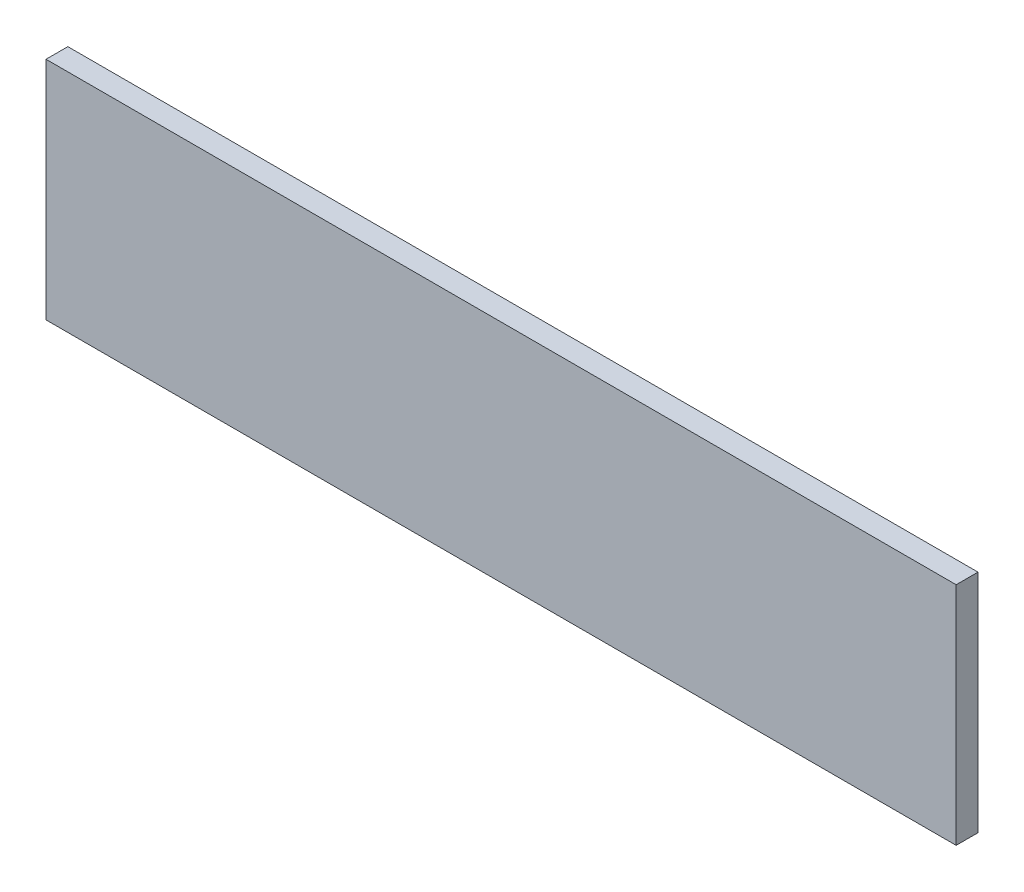
SolidWorks part; units mm, degrees
ref_plane "Plan de face" through (0, 0, 0) normal (0, 0, 1) x (1, 0, 0)
ref_plane "Plan de dessus" through (0, 0, 0) normal (0, 1, 0) x (1, 0, 0)
ref_plane "Plan de droite" through (0, 0, 0) normal (1, 0, 0) x (0, 0, -1)
sketch "Esquisse1" plane through (0, 0, 0) normal (0, 0, 1) x (1, 0, 0)
  line L1 (-62.5, 15.5) -> (62.5, 15.5)
  line L2 (-62.5, 15.5) -> (-62.5, -15.5)
  line L3 (-62.5, -15.5) -> (62.5, -15.5)
  line L4 (62.5, 15.5) -> (62.5, -15.5)
  line L5 (-62.5, 15.5) -> (62.5, -15.5) construction
  line L6 (-62.5, -15.5) -> (62.5, 15.5) construction
  point P0 (0, 0)
  dimension "D1" = 125
  dimension "D2" = 31
extrude "Boss.-Extru.1" add sketch "Esquisse1" along normal blind 3
